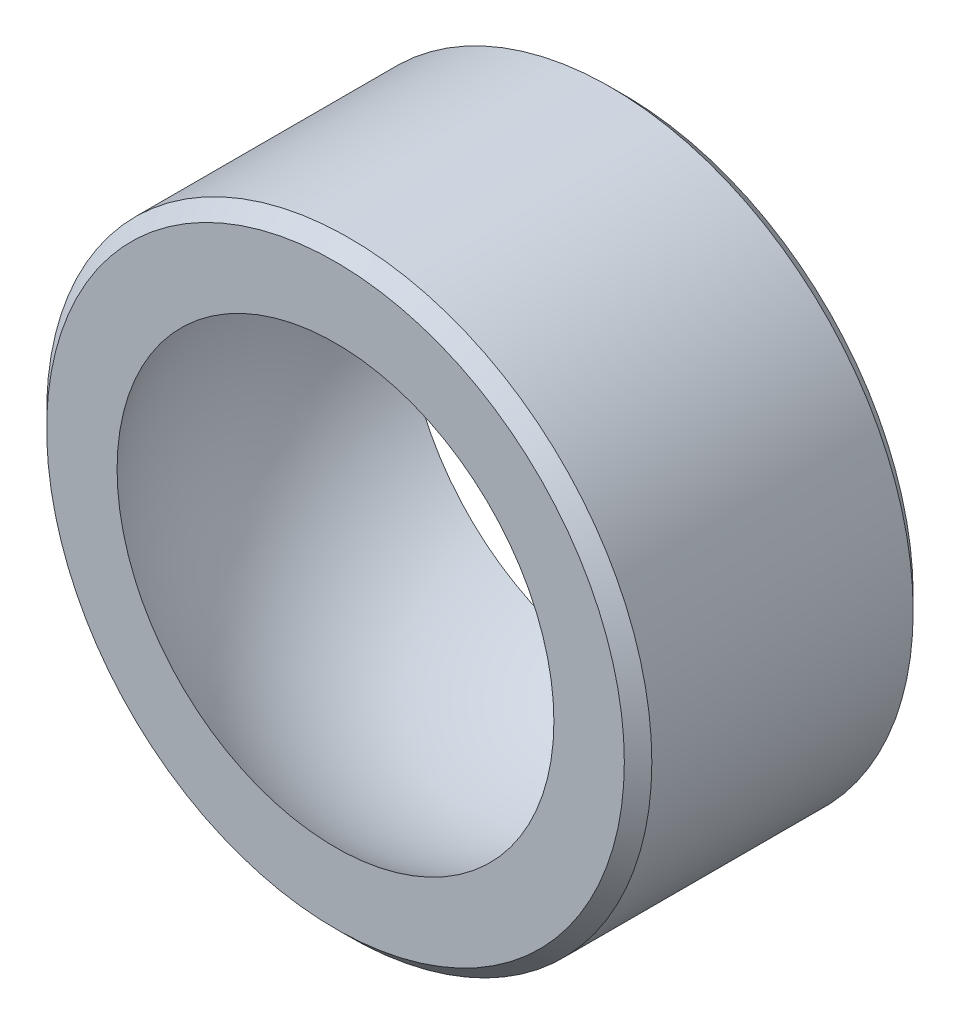
SolidWorks part; units mm, degrees
material "AISI 316 Stainless Steel Sheet (SS)"
ref_plane "Front Plane" through (0, 0, 0) normal (0, 0, 1) x (1, 0, 0)
ref_plane "Top Plane" through (0, 0, 0) normal (0, 1, 0) x (1, 0, 0)
ref_plane "Right Plane" through (0, 0, 0) normal (1, 0, 0) x (0, 0, -1)
sketch "Sketch2" plane through (0, 0, 0) normal (0, 0, 1) x (1, 0, 0)
  circle A0 centre (0, 0) radius 11
  dimension "D1" = 22
extrude "Boss-Extrude1" add sketch "Sketch2" along normal mid plane 10.5
sketch "Sketch4" plane through (0, 0, 0) normal (1, 0, 0) x (0, 0, -1)
  line L0 (0, 0) -> (50000, 0) construction
  line L1 (0, 9.5185) -> (0, -9.5185) construction
  line L2 (-7, -6.45) -> (7, -6.45) construction
  line L3 (7, -6.45) -> (7, 6.45) construction
  line L4 (7, -6.45) -> (7, 0)
  line L5 (7, 0) -> (-7, 0)
  line L6 (-7, 0) -> (-7, -6.45)
  circle A0 centre (0, 0) radius 9.5185 construction
  arc A1 (7, -6.45) -> (-7, -6.45) centre (0, 0) cw
  dimension "D1" = 14
  dimension "D2" = 12.9
revolve "Cut-Revolve1" cut sketch "Sketch4" angle 360 about L5
chamfer "Chamfer1" distance 0.5 angle 45 2 edges at (11, 0, 5.25) (11, 0, -5.25)
